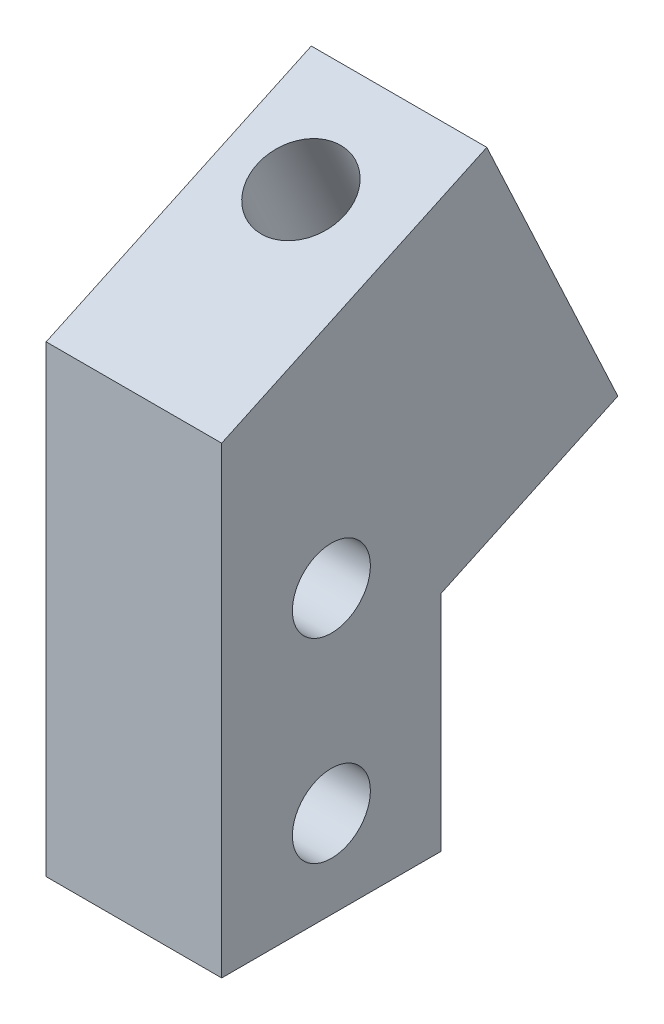
SolidWorks part; units mm, degrees
ref_plane "Front Plane" through (0, 0, 0) normal (0, 0, 1) x (1, 0, 0)
ref_plane "Top Plane" through (0, 0, 0) normal (0, 1, 0) x (1, 0, 0)
ref_plane "Right Plane" through (0, 0, 0) normal (1, 0, 0) x (0, 0, -1)
sketch "Sketch1" plane through (0, 0, 0) normal (1, 0, 0) x (0, 0, -1)
  line L0 (-11.25, 23.75) -> (15.9392, 36.4285)
  line L1 (-11.25, -23.75) -> (11.25, -23.75)
  line L2 (-11.25, -23.75) -> (-11.25, 23.75)
  line L4 (11.25, -23.75) -> (11.25, -0.8394)
  line L5 (-11.25, -23.75) -> (3.4476, 7.2783) construction
  line L6 (-11.25, 23.75) -> (11.25, -23.75) construction
  line L7 (0, -23.75) -> (0, 18.9005) construction
  line L8 (15.9392, 36.4285) -> (29.3762, 7.613)
  line L9 (29.3762, 7.613) -> (11.25, -0.8394)
  circle A0 centre (0, -14.75) radius 4
  circle A1 centre (0, 5.25) radius 4
  point P0 (0, 0)
  point P6 (0, 0)
  point P7 (0, 0)
  point P14 (-17.8234, 41.5739)
  point P18 (0, 0)
  point P20 (-12.0139, 23.75)
  dimension "D4" = 8
  dimension "D5" = 9
  dimension "D6" = 8
  dimension "D7" = 20
  dimension "D1" = 22.5
  dimension "D2" = 25
  dimension "D3" = 20
  dimension "D8" = 30
  dimension "D11" = 47.5
extrude "Boss-Extrude1" add sketch "Sketch1" along normal blind 18
sketch "Sketch2" plane through (0, 23.8171, 11.1061) normal (0, 0.9063, 0.4226) x (1, 0, 0)
  line L2 (18, 29.8412) -> (18, -0.1588) construction
  line L3 (18, -0.1588) -> (0, -0.1588) construction
  circle A0 centre (8, 19.8412) radius 4.5
  dimension "D1" = 9
  dimension "D2" = 20
  dimension "D3" = 10
extrude "Cut-Extrude1" cut sketch "Sketch2" against normal through all
